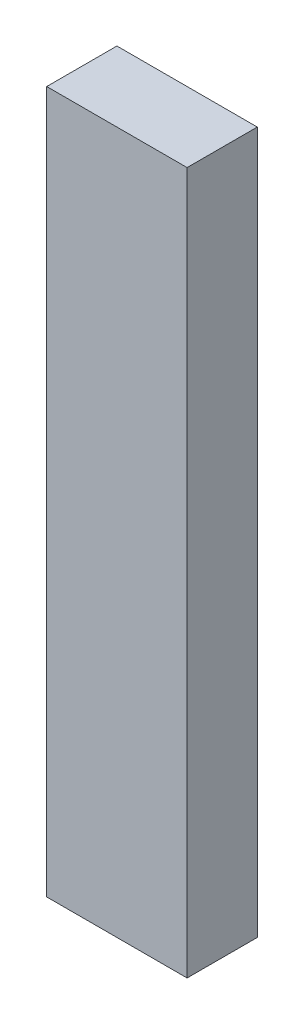
SolidWorks part; units mm, degrees
material "AISI 1045 Steel, cold drawn"
ref_plane "Front Plane" through (0, 0, 0) normal (0, 0, 1) x (1, 0, 0)
ref_plane "Top Plane" through (0, 0, 0) normal (0, 1, 0) x (1, 0, 0)
ref_plane "Right Plane" through (0, 0, 0) normal (1, 0, 0) x (0, 0, -1)
sketch "Sketch1" plane through (0, 0, 0) normal (0, 0, 1) x (1, 0, 0)
  line L1 (0, 0) -> (25.4, 0)
  line L2 (0, 0) -> (0, 127)
  line L3 (0, 127) -> (25.4, 127)
  line L4 (25.4, 0) -> (25.4, 127)
  dimension "D1" = 25.4
  dimension "D2" = 127
extrude "Extrude1" add sketch "Sketch1" along normal blind 12.7
ref_plane "Plane1" through (0, 152.4, 0) normal (0, 1, 0) x (-1, 0, 0)
sketch "Sketch2" plane through (0, 152.4, 0) normal (0, 1, 0) x (-1, 0, 0)
  line L0 (-12.7, 0) -> (-12.7, 12.7)
  line L1 (-25.4, 0) -> (0, 0) construction
  line L2 (-25.4, 12.7) -> (0, 12.7) construction
split line "Split Line1"
